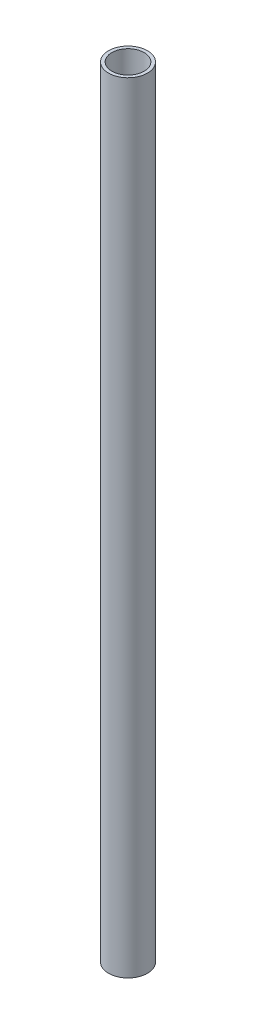
SolidWorks part; units mm, degrees
ref_plane "Front Plane" through (0, 0, 0) normal (0, 0, 1) x (1, 0, 0)
ref_plane "Top Plane" through (0, 0, 0) normal (0, 1, 0) x (1, 0, 0)
ref_plane "Right Plane" through (0, 0, 0) normal (1, 0, 0) x (0, 0, -1)
sketch "Sketch1" plane through (0, 0, 0) normal (0, 1, 0) x (1, 0, 0)
  circle A0 centre (0, 0) radius 21.082
  circle A1 centre (0, 0) radius 17.526
  dimension "D1" = 42.164
  dimension "D2" = 35.052
extrude "Boss-Extrude1" add sketch "Sketch1" along normal blind 844.55
